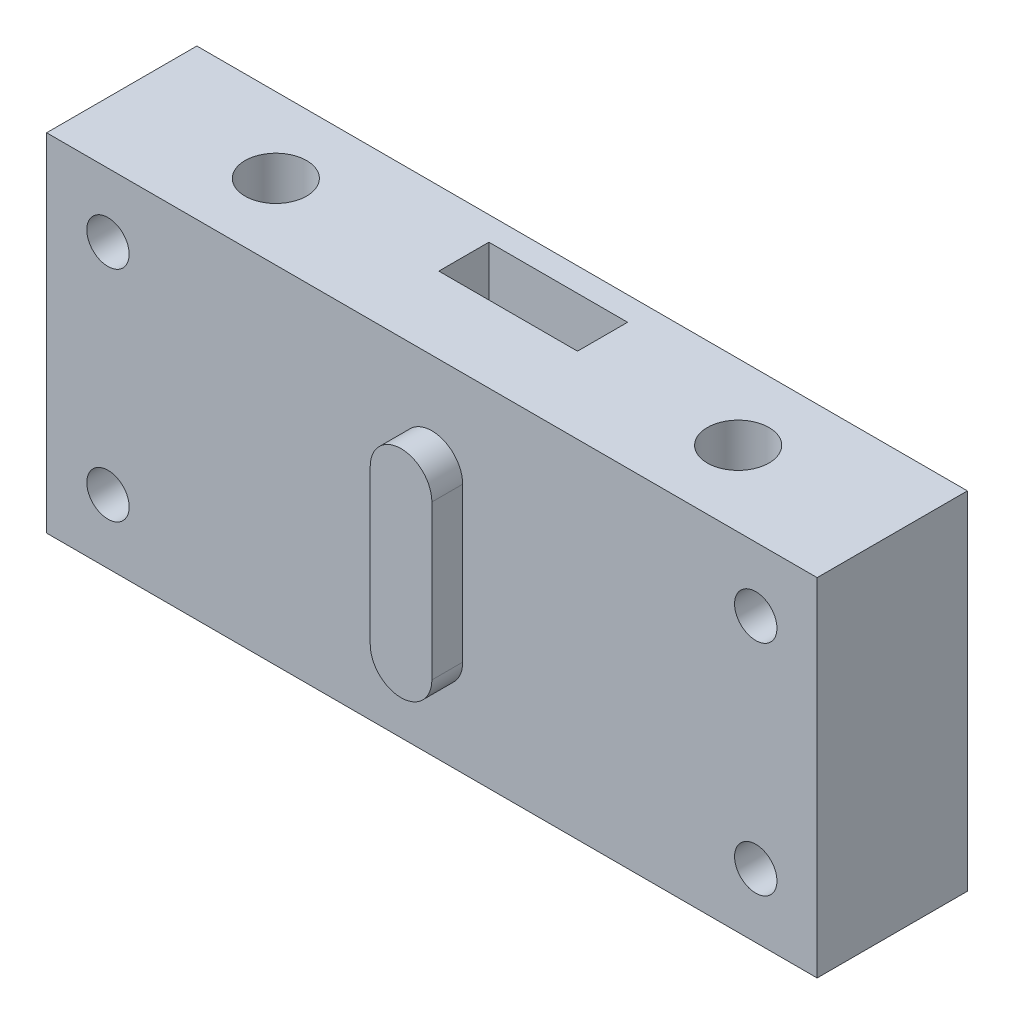
SolidWorks part; units mm, degrees
ref_plane "Front Plane" through (0, 0, 0) normal (0, 0, 1) x (1, 0, 0)
ref_plane "Top Plane" through (0, 0, 0) normal (0, 1, 0) x (1, 0, 0)
ref_plane "Right Plane" through (0, 0, 0) normal (1, 0, 0) x (0, 0, -1)
sketch "Sketch1" plane through (0, 0, 0) normal (0, 0, 1) x (1, 0, 0)
  line L1 (50, 22.5) -> (-50, 22.5)
  line L2 (50, 22.5) -> (50, -22.5)
  line L3 (50, -22.5) -> (-50, -22.5)
  line L4 (-50, 22.5) -> (-50, -22.5)
  line L5 (50, 22.5) -> (-50, -22.5) construction
  line L6 (50, -22.5) -> (-50, 22.5) construction
  point P0 (0, 0)
  dimension "D1" = 100
  dimension "D2" = 45
extrude "Boss-Extrude1" add sketch "Sketch1" along normal blind 19.5
sketch "Sketch2" plane through (0, 22.5, 0) normal (0, 1, 0) x (1, 0, 0)
  line L2 (0, 0) -> (0, -19.5) construction
  line L3 (50, -19.5) -> (-50, -19.5) construction
  line L5 (50, -9.75) -> (-50, -9.75) construction
  line L6 (50, -19.5) -> (50, 0) construction
  line L7 (-50, -19.5) -> (-50, 0) construction
  circle A0 centre (-30, -9.75) radius 4
  circle A1 centre (30, -9.75) radius 4
  dimension "D1" = 60
  dimension "D3" = 8
extrude "Cut-Extrude1" cut sketch "Sketch2" against normal through all
sketch "Sketch4" plane through (0, 0, 0) normal (0, 0, -1) x (-1, 0, 0)
  line L0 (0, 0) -> (0, 17.8306) construction
  circle A0 centre (-42.0348, 14.2) radius 2.75
  circle A1 centre (-42.0348, -14.2) radius 2.75
  circle A2 centre (42.0348, -14.2) radius 2.75
  circle A3 centre (42.0348, 14.2) radius 2.75
  dimension "D1" = 5.5
extrude "Cut-Extrude3" cut sketch "Sketch4" against normal through all
sketch "Sketch5" plane through (0, 22.5, 0) normal (0, 1, 0) x (1, 0, 0)
  line L0 (50, -19.5) -> (-50, -19.5) construction
  line L1 (-9, -9.6) -> (9, -9.6)
  line L2 (-9, -9.6) -> (-9, -3.1)
  line L3 (-9, -3.1) -> (9, -3.1)
  line L4 (9, -9.6) -> (9, -3.1)
  line L5 (0, 0) -> (0, -19.5) construction
  line L6 (50, 0) -> (-50, 0) construction
  line L7 (-50, -19.5) -> (-50, 0) construction
  dimension "D1" = 3.1
  dimension "D2" = 41
  dimension "D3" = 6.5
extrude "Cut-Extrude5" cut sketch "Sketch5" against normal through all
sketch "Sketch6" plane through (0, 0, 0) normal (0, 0, -1) x (-1, 0, 0)
  line L0 (9, -22.5) -> (9, 22.5) construction
  line L1 (-9, 5) -> (9, 5)
  line L2 (-9, 5) -> (-9, -5)
  line L3 (-9, -5) -> (9, -5)
  line L4 (9, 5) -> (9, -5)
  line L5 (-9, 5) -> (9, -5) construction
  line L6 (-9, -5) -> (9, 5) construction
  point P0 (0, 0)
  dimension "D1" = 10
extrude "Cut-Extrude6" cut sketch "Sketch6" against normal blind 4
sketch "Sketch7" plane through (0, 0, 19.5) normal (0, 0, 1) x (1, 0, 0)
  line L0 (0, 0) -> (50, 0) construction
  line L1 (50, -22.5) -> (50, 22.5) construction
  line L2 (0, 10) -> (0, -10) construction
  line L3 (4, 10) -> (4, -10)
  line L4 (-4, 10) -> (-4, -10)
  arc A0 (4, 10) -> (-4, 10) centre (0, 10) ccw
  arc A1 (-4, -10) -> (4, -10) centre (0, -10) ccw
  point P7 (0, 0)
  dimension "D2" = 28
  dimension "D1" = 8
extrude "Boss-Extrude2" add sketch "Sketch7" along normal blind 4
